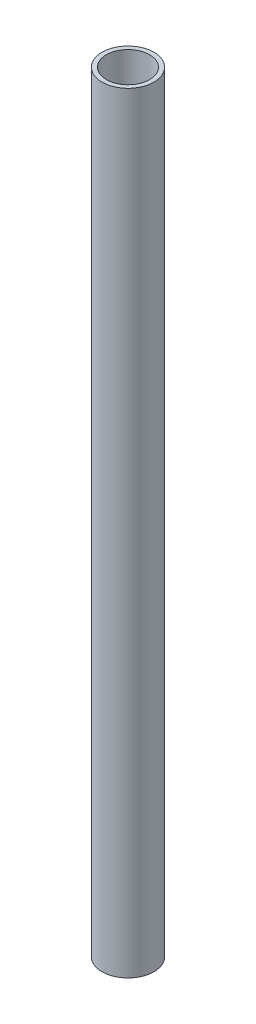
SolidWorks part; units mm, degrees
material "AISI 304"
ref_plane "前视基准面" through (0, 0, 0) normal (0, 0, 1) x (1, 0, 0)
ref_plane "上视基准面" through (0, 0, 0) normal (0, 1, 0) x (1, 0, 0)
ref_plane "右视基准面" through (0, 0, 0) normal (1, 0, 0) x (0, 0, -1)
other "Configuration Table"
sketch "草图1" plane through (0, 0, 0) normal (0, 1, 0) x (1, 0, 0)
  circle A0 centre (0, 0) radius 2.5
  circle A1 centre (0, 0) radius 3
  dimension "D1" = 5
  dimension "D2" = 6
extrude "凸台-拉伸1" add sketch "草图1" along normal blind 89.19
